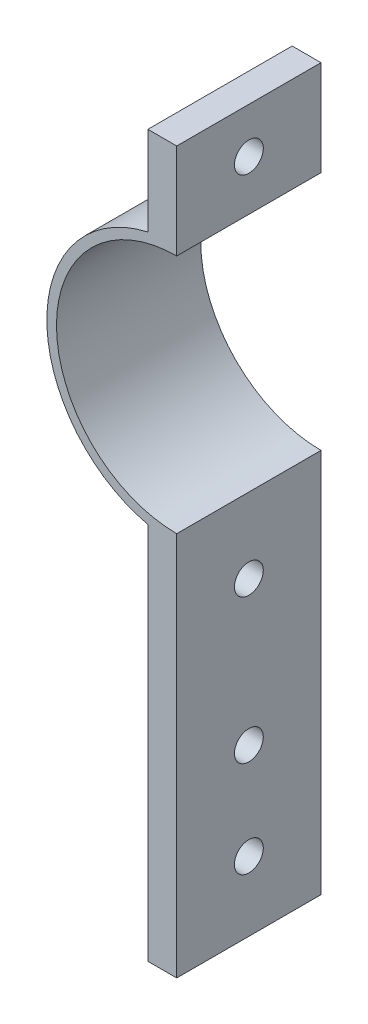
SolidWorks part; units mm, degrees
ref_plane "前视基准面" through (0, 0, 0) normal (0, 0, 1) x (1, 0, 0)
ref_plane "上视基准面" through (0, 0, 0) normal (0, 1, 0) x (1, 0, 0)
ref_plane "右视基准面" through (0, 0, 0) normal (1, 0, 0) x (0, 0, -1)
sketch "草图1" plane through (0, 0, 0) normal (0, 0, 1) x (1, 0, 0)
  line L0 (-3, 13.1624) -> (-3, 22.4052)
  line L1 (0, 12.5) -> (0, 22.4052)
  line L2 (-3, -13.1624) -> (-3, -52.5)
  line L4 (0, 22.4052) -> (-3, 22.4052)
  line L5 (0, -12.5) -> (0, -52.5)
  line L6 (0, -52.5) -> (-3, -52.5)
  arc A0 (0, 12.5) -> (0, -12.5) centre (0, 0) ccw
  arc A1 (-13.5, 0) -> (-3, 13.1624) centre (0, 0) cw
  arc A2 (-13.5, 0) -> (-3, -13.1624) centre (0, 0) ccw
extrude "凸台-拉伸1" add sketch "草图1" along normal blind 15
ref_plane "基准面1" through (-3, 0, 0) normal (-1, 0, 0) x (0, 0, 1)
sketch "草图2" plane through (-3, 0, 0) normal (-1, 0, 0) x (0, 0, 1)
  circle A0 centre (7.5, 17.6967) radius 1.5
  circle A2 centre (7.5, -20.2915) radius 1.5
  circle A6 centre (7.5, -35.2915) radius 1.5
  circle A9 centre (7.5, -45.2915) radius 1.5
extrude "切除-拉伸1" cut sketch "草图2" against normal blind 20
